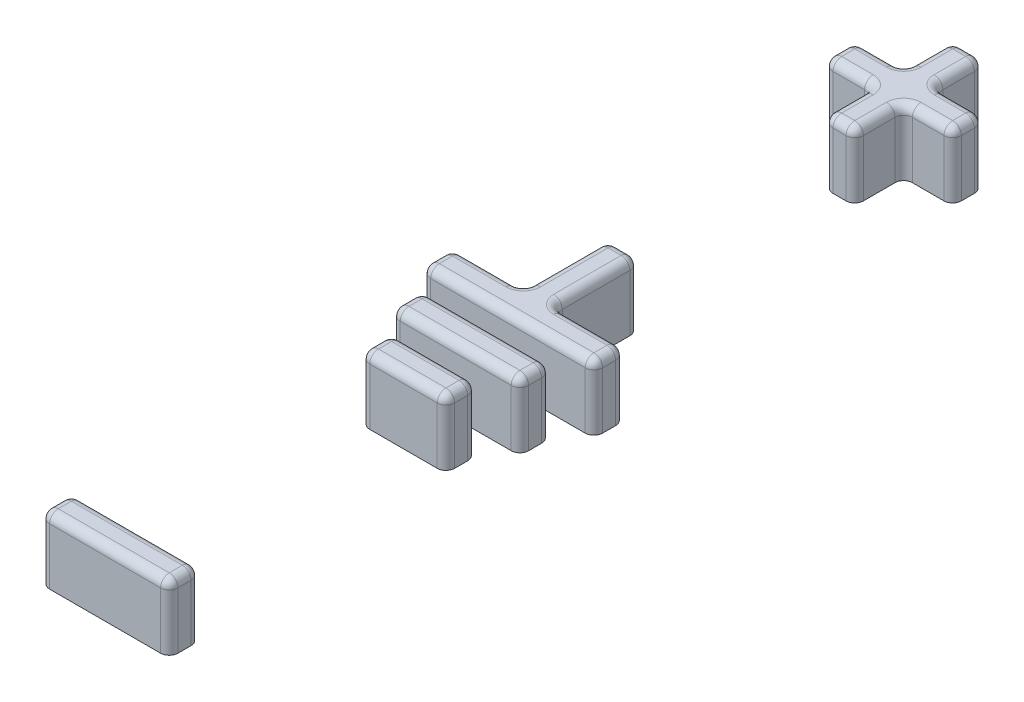
SolidWorks part; units mm, degrees
ref_plane "Front Plane" through (0, 0, 0) normal (0, 0, 1) x (1, 0, 0)
ref_plane "Top Plane" through (0, 0, 0) normal (0, 1, 0) x (1, 0, 0)
ref_plane "Right Plane" through (0, 0, 0) normal (1, 0, 0) x (0, 0, -1)
sketch "Sketch3" plane through (0, 0, 0) normal (0, 1, 0) x (1, 0, 0)
  line L0 (12.95, 18.1856) -> (0, 18.1856) construction
  line L1 (-0.7, 15.2356) -> (0.7, 15.2356)
  line L2 (-0.7, 15.2356) -> (-0.7, 17.4856)
  line L3 (-0.7, 21.1356) -> (0.7, 21.1356)
  line L4 (0.7, 15.2356) -> (0.7, 17.4856)
  line L5 (-0.7, 15.2356) -> (0.7, 21.1356) construction
  line L6 (-0.7, 21.1356) -> (0.7, 15.2356) construction
  line L7 (-2.95, 17.4856) -> (-0.7, 17.4856)
  line L8 (-2.95, 17.4856) -> (-2.95, 18.8856)
  line L9 (-2.95, 18.8856) -> (-0.7, 18.8856)
  line L10 (2.95, 17.4856) -> (2.95, 18.8856)
  line L11 (-2.95, 17.4856) -> (2.95, 18.8856) construction
  line L12 (-2.95, 18.8856) -> (2.95, 17.4856) construction
  line L13 (0.7, 18.8856) -> (2.95, 18.8856)
  line L14 (-0.7, 18.8856) -> (-0.7, 21.1356)
  line L15 (0.7, 17.4856) -> (2.95, 17.4856)
  line L16 (0, 18.1856) -> (0, -17.8144) construction
  line L17 (0.7, 18.8856) -> (0.7, 21.1356)
  line L18 (0.7, 1.4) -> (3.95, 1.4)
  line L19 (-2.95, -18.5144) -> (2.95, -18.5144)
  line L20 (-2.95, -18.5144) -> (-2.95, -17.1144)
  line L21 (-2.95, -17.1144) -> (2.95, -17.1144)
  line L22 (2.95, -18.5144) -> (2.95, -17.1144)
  line L23 (-2.95, -18.5144) -> (2.95, -17.1144) construction
  line L24 (-2.95, -17.1144) -> (2.95, -18.5144) construction
  line L25 (-0.7, 1.4) -> (-0.7, 5.3)
  line L26 (-0.7, 5.3) -> (0.7, 5.3)
  line L27 (0.7, 1.4) -> (0.7, 5.3)
  line L28 (-0.7, 1.4) -> (0.7, 5.3) construction
  line L29 (-0.7, 5.3) -> (0.7, 1.4) construction
  line L30 (3.95, 1.4) -> (3.95, 0)
  line L31 (3.95, 0) -> (-3.95, 0)
  line L32 (-3.95, 0) -> (-3.95, 1.4)
  line L33 (-3.95, 1.4) -> (-0.7, 1.4)
  line L34 (-2.95, -2.4) -> (2.95, -2.4)
  line L35 (-2.95, -2.4) -> (-2.95, -1)
  line L36 (-2.95, -1) -> (2.95, -1)
  line L37 (2.95, -2.4) -> (2.95, -1)
  line L38 (-2.95, -2.4) -> (2.95, -1) construction
  line L39 (-2.95, -1) -> (2.95, -2.4) construction
  line L40 (-1.95, -4.8) -> (1.95, -4.8)
  line L41 (-1.95, -4.8) -> (-1.95, -3.4)
  line L42 (-1.95, -3.4) -> (1.95, -3.4)
  line L43 (1.95, -4.8) -> (1.95, -3.4)
  line L44 (-1.95, -4.8) -> (1.95, -3.4) construction
  line L45 (-1.95, -3.4) -> (1.95, -4.8) construction
  point P0 (0, 18.1856)
  point P5 (0, 18.1856)
  point P21 (8.5, -17.8144)
  point P22 (0, 3.35)
  point P27 (0, 0)
  point P32 (0, -4.1)
  point P34 (0, -1.7)
  dimension "D1" = 5.9
  dimension "D2" = 1.4
  dimension "D3" = 10
  dimension "D4" = 1.4
  dimension "D5" = 5.9
  dimension "D6" = 1.4
  dimension "D7" = 7.9
  dimension "D8" = 1.4
  dimension "D9" = 3.9
  dimension "D10" = 1.4
  dimension "D11" = 5.9
  dimension "D12" = 1
  dimension "D13" = 1
  dimension "D14" = 1.4
  dimension "D15" = 3.9
  dimension "D16" = 5.9
extrude "Boss-Extrude3" add sketch "Sketch3" along normal blind 3
fillet "Fillet1" radius 0.4 24 edges at (1.825, 3, -18.8856) (2.95, 3, -18.1856) (1.825, 3, -17.4856) (0.7, 3, -16.3606) (0, 3, -15.2356) (-0.7, 3, -16.3606) (-1.825, 3, -17.4856) (-2.95, 3, -18.1856) (-1.825, 3, -18.8856) (-0.7, 3, -20.0106) (0, 3, -21.1356) (0.7, 3, -20.0106) (-0.7, 1.5, -17.4856) (-2.95, 1.5, -17.4856) (-2.95, 1.5, -18.8856) (-0.7, 1.5, -18.8856) (-0.7, 1.5, -21.1356) (0.7, 1.5, -21.1356) (0.7, 1.5, -18.8856) (2.95, 1.5, -18.8856) (2.95, 1.5, -17.4856) (0.7, 1.5, -17.4856) (-0.7, 1.5, -15.2356) (0.7, 1.5, -15.2356)
fillet "Fillet2" radius 0.4 16 edges at (2.325, 3, -1.4) (3.95, 3, -0.7) (0, 3, 0) (-3.95, 3, -0.7) (-2.325, 3, -1.4) (-0.7, 3, -3.35) (0, 3, -5.3) (0.7, 3, -3.35) (-3.95, 1.5, 0) (-3.95, 1.5, -1.4) (-0.7, 1.5, -1.4) (-0.7, 1.5, -5.3) (0.7, 1.5, -5.3) (3.95, 1.5, 0) (3.95, 1.5, -1.4) (0.7, 1.5, -1.4)
fillet "Fillet3" radius 0.4 8 edges at (0, 3, 2.4) (-2.95, 3, 1.7) (0, 3, 1) (2.95, 3, 1.7) (2.95, 1.5, 1) (2.95, 1.5, 2.4) (-2.95, 1.5, 1) (-2.95, 1.5, 2.4)
fillet "Fillet4" radius 0.4 8 edges at (0, 3, 4.8) (-1.95, 3, 4.1) (0, 3, 3.4) (1.95, 3, 4.1) (-1.95, 1.5, 3.4) (-1.95, 1.5, 4.8) (1.95, 1.5, 3.4) (1.95, 1.5, 4.8)
fillet "Fillet5" radius 0.4 8 edges at (0, 3, 18.5144) (-2.95, 3, 17.8144) (0, 3, 17.1144) (2.95, 3, 17.8144) (2.95, 1.5, 17.1144) (2.95, 1.5, 18.5144) (-2.95, 1.5, 18.5144) (-2.95, 1.5, 17.1144)
